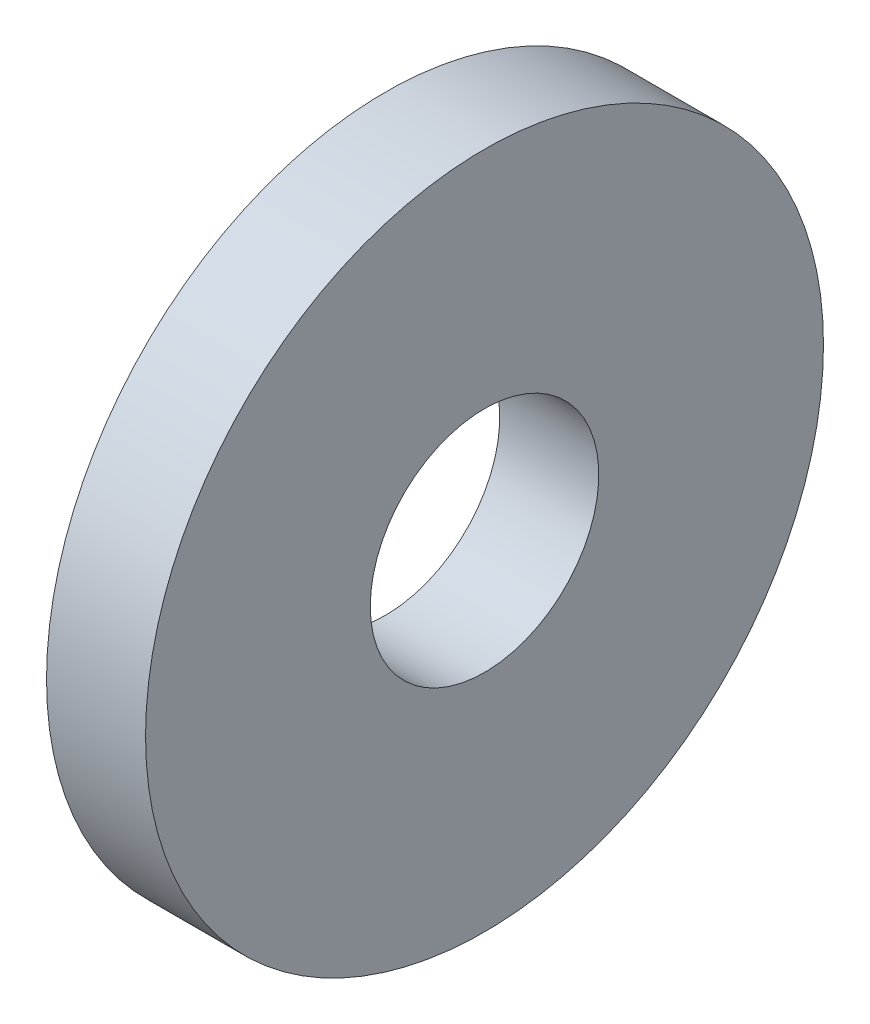
SolidWorks part; units mm, degrees
material "Plain Carbon Steel"
ref_plane "Front Plane" through (0, 0, 0) normal (0, 0, 1) x (1, 0, 0)
ref_plane "Top Plane" through (0, 0, 0) normal (0, 1, 0) x (1, 0, 0)
ref_plane "Right Plane" through (0, 0, 0) normal (1, 0, 0) x (0, 0, -1)
sketch "Sketch1" plane through (0, 0, 0) normal (0, 0, 1) x (1, 0, 0)
  line L0 (-18.0268, 0) -> (18.0268, 0) construction
  line L2 (0, 1.5) -> (1.3, 1.5)
  line L3 (0, 1.5) -> (0, 4.45)
  line L4 (0, 4.45) -> (1.3, 4.45)
  line L5 (1.3, 1.5) -> (1.3, 4.45)
  dimension "D1" = 3
  dimension "D2" = 8.9
  dimension "D3" = 1.3
revolve "Revolve1" add sketch "Sketch1" angle 360 about L0
